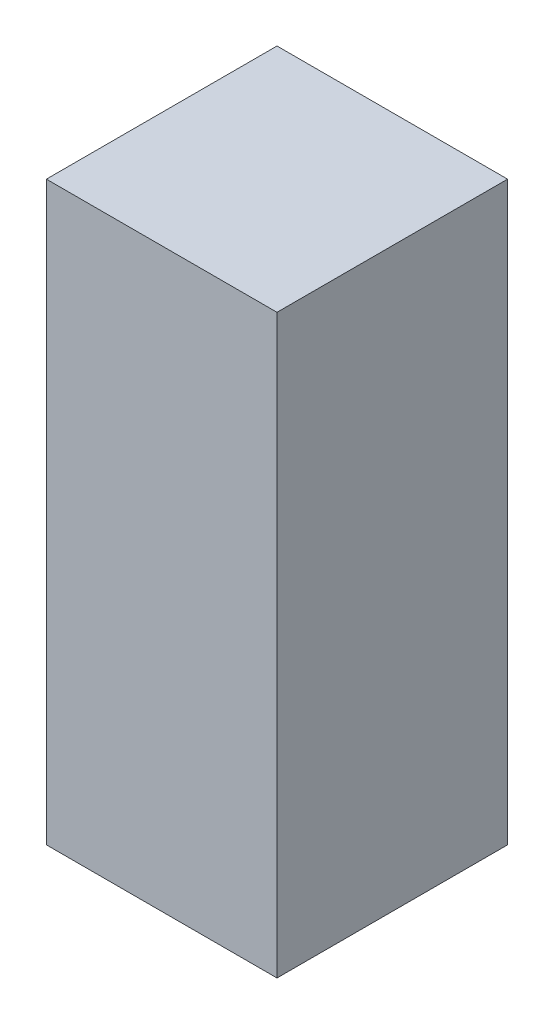
SolidWorks part; units mm, degrees
ref_plane "Front Plane" through (0, 0, 0) normal (0, 0, 1) x (1, 0, 0)
ref_plane "Top Plane" through (0, 0, 0) normal (0, 1, 0) x (1, 0, 0)
ref_plane "Right Plane" through (0, 0, 0) normal (1, 0, 0) x (0, 0, -1)
sketch "Sketch1" plane through (0, 0, 0) normal (0, 1, 0) x (1, 0, 0)
  line L1 (-3.81, -3.81) -> (3.81, -3.81)
  line L2 (-3.81, -3.81) -> (-3.81, 3.81)
  line L3 (-3.81, 3.81) -> (3.81, 3.81)
  line L4 (3.81, -3.81) -> (3.81, 3.81)
  line L5 (-3.81, -3.81) -> (3.81, 3.81) construction
  line L6 (-3.81, 3.81) -> (3.81, -3.81) construction
  point P0 (0, 0)
  dimension "D1" = 7.62
  dimension "D2" = 7.62
extrude "Boss-Extrude1" add sketch "Sketch1" along normal blind 19.05
sketch "Sketch2" plane through (0, 0, 3.81) normal (0, 0, 1) x (1, 0, 0)
  line L0 (3.81, 9.525) -> (-3.81, 9.525) construction
  line L1 (3.0161, 3.2774) -> (-3.0161, 3.2774)
  line L2 (3.0161, 3.2774) -> (3.0161, 15.7726)
  line L3 (3.0161, 15.7726) -> (-3.0161, 15.7726)
  line L4 (-3.0161, 3.2774) -> (-3.0161, 15.7726)
  line L5 (3.0161, 3.2774) -> (-3.0161, 15.7726) construction
  line L6 (3.0161, 15.7726) -> (-3.0161, 3.2774) construction
  line L7 (3.81, 19.05) -> (3.81, 0) construction
  line L8 (-3.81, 19.05) -> (-3.81, 0) construction
  point P0 (0, 9.525)
  point P11 (0, 9.525)
  point P12 (0, 0)
  point P13 (0, 9.525)
  point P14 (0, 9.525)
  point P15 (5.5998, 8.0011)
extrude "Cut-Extrude1" cut sketch "Sketch2" against normal through all
sketch "Sketch4" plane through (0, 0, 3.81) normal (0, 0, 1) x (1, 0, 0)
  line L1 (-3.81, 19.05) -> (3.81, 19.05)
  line L2 (-3.81, 19.05) -> (-3.81, 0)
  line L3 (-3.81, 0) -> (3.81, 0)
  line L4 (3.81, 19.05) -> (3.81, 0)
extrude "Boss-Extrude3" add sketch "Sketch4" against normal blind 0.762
sketch "Sketch9" plane through (-3.0161, 0, 0) normal (1, 0, 0) x (0, 0, -1)
  line L0 (-3.048, 6.0118) -> (1.3236, 6.0118)
  line L1 (-3.048, 3.2774) -> (1.3236, 3.2774)
  line L2 (-3.048, 3.2774) -> (-3.048, 4.5474)
  line L3 (-3.048, 4.5474) -> (1.3236, 4.5474)
  line L4 (1.3236, 3.2774) -> (1.3236, 4.5474)
  line L5 (-3.048, 6.0118) -> (-3.048, 7.2818)
  line L6 (-3.048, 7.2818) -> (1.3236, 7.2818)
  line L7 (1.3236, 6.0118) -> (1.3236, 7.2818)
  line L8 (-3.048, 8.7462) -> (1.3236, 8.7462)
  line L9 (-3.048, 8.7462) -> (-3.048, 10.0162)
  line L10 (-3.048, 10.0162) -> (1.3236, 10.0162)
  line L11 (1.3236, 8.7462) -> (1.3236, 10.0162)
  line L12 (-3.048, 11.4805) -> (1.3236, 11.4805)
  line L13 (-3.048, 11.4805) -> (-3.048, 12.7505)
  line L14 (-3.048, 12.7505) -> (1.3236, 12.7505)
  line L15 (1.3236, 11.4805) -> (1.3236, 12.7505)
  line L16 (-3.048, 3.2774) -> (-3.048, 15.7726) construction
  dimension "D1" = 1.27
  dimension "D2" = 1.27
  dimension "D3" = 1.27
  dimension "D4" = 1.27
  dimension "D5" = 4.3716
  dimension "D6" = 4.3716
  dimension "D7" = 4.3716
  dimension "D8" = 4.3716
  dimension "D9" = 1.4644
  dimension "D10" = 1.4644
  dimension "D11" = 1.4644
equation "\"D2@Sketch9\"=\"D1@Sketch9\""
equation "\"D3@Sketch9\"=\"D1@Sketch9\""
equation "\"D4@Sketch9\"=\"D1@Sketch9\""
equation "\"D6@Sketch9\"=\"D5@Sketch9\""
equation "\"D7@Sketch9\"=\"D5@Sketch9\""
equation "\"D8@Sketch9\"=\"D5@Sketch9\""
equation "\"D10@Sketch9\"=\"D9@Sketch9\""
equation "\"D11@Sketch9\"=\"D9@Sketch9\""
